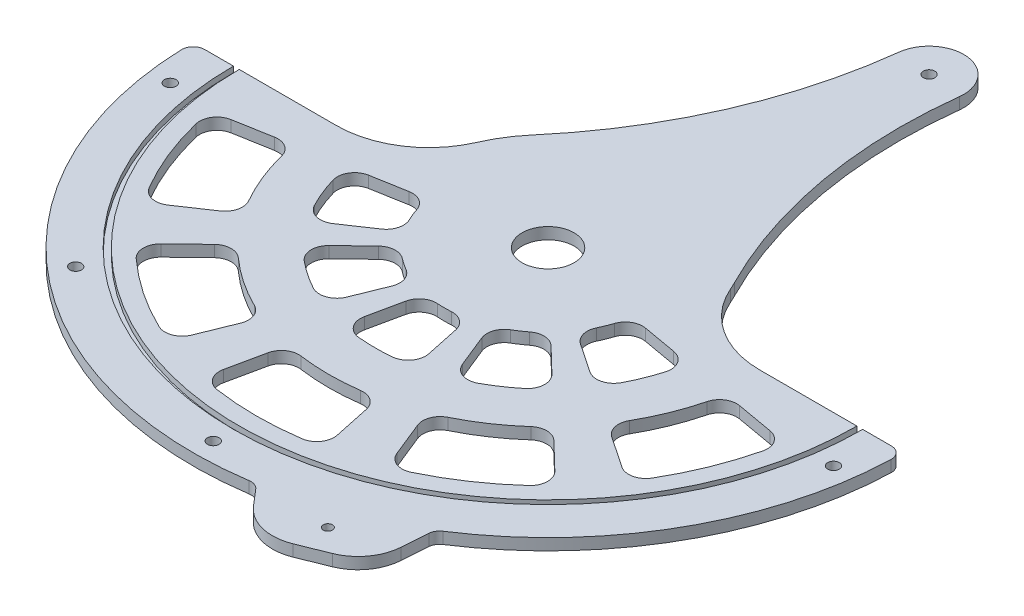
SolidWorks part; units mm, degrees
material "Polycarbonate"
ref_plane "Front Plane" through (0, 0, 0) normal (0, 0, 1) x (1, 0, 0)
ref_plane "Top Plane" through (0, 0, 0) normal (0, 1, 0) x (1, 0, 0)
ref_plane "Right Plane" through (0, 0, 0) normal (1, 0, 0) x (0, 0, -1)
sketch "Sketch1" plane through (0, 0, 0) normal (0, 1, 0) x (1, 0, 0)
  line L0 (76.2, 0) -> (173.0375, 0)
  line L3 (-173.0375, 0) -> (-76.2, 0)
  arc A0 (-169.8625, 0) -> (169.8625, 0) centre (0, 0) ccw construction
  arc A1 (173.0375, 0) -> (-173.0375, 0) centre (0, 0) cw
  arc A2 (-76.2, 0) -> (76.2, 0) centre (0, 0) cw
  dimension "D1" = 169.8625
  dimension "D2" = 3.175
  dimension "D4" = 76.2
extrude "Boss-Extrude1" add sketch "Sketch1" along normal mid plane 6.35
sketch "Sketch2" plane through (0, 3.175, 0) normal (0, 1, 0) x (1, 0, 0)
  line L0 (-76.2, 0) -> (-173.0375, 0) construction
  line L2 (173.0375, 0) -> (76.2, 0) construction
  line L3 (-78.9658, -53.2631) -> (-47.3795, -31.9579)
  line L4 (-56.2818, -9.924) -> (-93.8029, -16.54)
  line L5 (-60.0635, -148.6623) -> (-45.1963, -111.8647)
  line L6 (-157.9016, -27.8423) -> (-132.9258, -89.6596) construction
  line L7 (-86.7883, -83.8105) -> (-115.3371, -111.3798)
  line L8 (-35.6813, -88.3143) -> (-21.4088, -52.9886)
  line L9 (-41.1103, -39.6997) -> (-68.5171, -66.1662)
  line L10 (-132.9258, -89.6596) -> (-100.0234, -67.4666)
  line L11 (-118.8171, -20.9507) -> (-157.9016, -27.8423)
  line L12 (33.336, -156.8337) -> (25.0845, -118.0135)
  line L13 (-118.8171, -20.9507) -> (-100.0234, -67.4666) construction
  line L14 (-25.0845, -118.0135) -> (-33.336, -156.8337)
  line L15 (19.8036, -93.1686) -> (11.8822, -55.9011)
  line L16 (-11.8822, -55.9011) -> (-19.8036, -93.1686)
  line L17 (115.3371, -111.3798) -> (86.7883, -83.8105)
  line L18 (45.1963, -111.8647) -> (60.0635, -148.6623)
  line L19 (68.5171, -66.1662) -> (41.1103, -39.6997)
  line L20 (21.4088, -52.9886) -> (35.6813, -88.3143)
  line L21 (157.9016, -27.8423) -> (118.8171, -20.9507)
  line L22 (100.0234, -67.4666) -> (132.9258, -89.6596)
  line L23 (93.8029, -16.54) -> (56.2818, -9.924)
  line L24 (47.3795, -31.9579) -> (78.9658, -53.2631)
  line L25 (157.9016, -14.9611) -> (157.9016, -27.8423) construction
  line L26 (157.9016, -27.8423) -> (170.7829, -27.8423) construction
  line L27 (-30.1025, -103.6679) -> (0, 0) construction
  line L28 (-111.8647, -45.1963) -> (-88.3143, -35.6813) construction
  arc A0 (-157.9016, -27.8423) -> (-132.9258, -89.6596) centre (0, 0) ccw
  arc A1 (-93.8029, -16.54) -> (-78.9658, -53.2631) centre (0, 0) ccw
  arc A2 (-56.2818, -9.924) -> (-47.3795, -31.9579) centre (0, 0) ccw
  arc A3 (-86.7883, -83.8105) -> (-45.1963, -111.8647) centre (0, 0) ccw
  arc A4 (-173.0375, 0) -> (173.0375, 0) centre (0, 0) ccw construction
  arc A5 (-118.8171, -20.9507) -> (-100.0234, -67.4666) centre (0, 0) ccw
  arc A6 (-115.3371, -111.3798) -> (-60.0635, -148.6623) centre (0, 0) ccw
  arc A7 (-68.5171, -66.1662) -> (-35.6813, -88.3143) centre (0, 0) ccw
  arc A8 (-41.1103, -39.6997) -> (-21.4088, -52.9886) centre (0, 0) ccw
  arc A9 (-25.0845, -118.0135) -> (25.0845, -118.0135) centre (0, 0) ccw
  arc A10 (-33.336, -156.8337) -> (33.336, -156.8337) centre (0, 0) ccw
  arc A11 (-19.8036, -93.1686) -> (19.8036, -93.1686) centre (0, 0) ccw
  arc A12 (-11.8822, -55.9011) -> (11.8822, -55.9011) centre (0, 0) ccw
  arc A13 (45.1963, -111.8647) -> (86.7883, -83.8105) centre (0, 0) ccw
  arc A14 (60.0635, -148.6623) -> (115.3371, -111.3798) centre (0, 0) ccw
  arc A15 (35.6813, -88.3143) -> (68.5171, -66.1662) centre (0, 0) ccw
  arc A16 (21.4088, -52.9886) -> (41.1103, -39.6997) centre (0, 0) ccw
  arc A17 (100.0234, -67.4666) -> (118.8171, -20.9507) centre (0, 0) ccw
  arc A18 (132.9258, -89.6596) -> (157.9016, -27.8423) centre (0, 0) ccw
  arc A19 (78.9658, -53.2631) -> (93.8029, -16.54) centre (0, 0) ccw
  arc A20 (47.3795, -31.9579) -> (56.2818, -9.924) centre (0, 0) ccw
  arc A21 (-173.0375, 0) -> (173.0375, 0) centre (0, 0) ccw construction
  circle A22 centre (0, 0) radius 50.8 construction
  circle A23 centre (-30.1025, -103.6679) radius 61.9125 construction
  circle A24 centre (-13.5019, -46.4981) radius 2.3813 construction
  circle A25 centre (0, 0) radius 107.95 construction
  point P51 (0, 0)
  point P54 (0, 0)
  point P66 (-100.0895, -40.4388)
  dimension "D1" = 12.7
  dimension "D2" = 10
  dimension "D3" = 10
  dimension "D5" = 25.4
  dimension "D6" = 57.15
  dimension "D4" = 101.6
  dimension "D8" = 123.825
  dimension "D9" = 4.7625
  dimension "D10" = 10
  dimension "D7" = 5
extrude "Cut-Extrude1" cut sketch "Sketch2" against normal through all
sketch "Sketch4" plane through (0, 0, 0) normal (0, 1, 0) x (1, 0, 0)
  line L0 (173.0375, 0) -> (195.2625, 0)
  line L4 (-195.2625, 0) -> (-173.0375, 0)
  arc A0 (-195.2625, 0) -> (195.2625, 0) centre (0, 0) ccw
  arc A1 (-173.0375, 0) -> (173.0375, 0) centre (0, 0) ccw construction
  arc A2 (-173.0375, 0) -> (173.0375, 0) centre (0, 0) ccw
  dimension "D1" = 22.225
sketch "Sketch5" plane through (0, 3.175, 0) normal (0, 1, 0) x (1, 0, 0)
  line L0 (-76.2, 0) -> (-173.0375, 0) construction
  line L1 (169.8625, 0) -> (173.0375, 0)
  line L6 (-169.8625, 0) -> (-173.0375, 0)
  arc A0 (-169.8625, 0) -> (169.8625, 0) centre (0, 0) ccw
  arc A1 (-173.0375, 0) -> (173.0375, 0) centre (0, 0) ccw construction
  arc A2 (-173.0375, 0) -> (173.0375, 0) centre (0, 0) ccw
  dimension "D1" = 3.175
extrude "Cut-Extrude2" cut sketch "Sketch5" against normal blind 3.175
extrude "Boss-Extrude2" add sketch "Sketch4" against normal mid plane 6.35 contours A0 L0 A2 L4
sketch "Sketch6" plane through (0, 3.175, 0) normal (0, 1, 0) x (1, 0, 0)
  circle A0 centre (0, 0) radius 14.2875
  dimension "D1" = 28.575
extrude "Cut-Extrude3" cut sketch "Sketch6" against normal through all
sketch "Sketch7" plane through (0, 3.175, 0) normal (0, 1, 0) x (1, 0, 0)
  line L0 (32.2069, -192.5881) -> (53.9687, -217.9881)
  line L1 (53.9687, -217.9881) -> (101.0697, -198.958)
  line L2 (101.0697, -198.958) -> (103.4662, -165.5965)
  line L4 (32.2069, -192.5881) -> (103.4662, -165.5965)
  arc A0 (-195.2625, 0) -> (195.2625, 0) centre (0, 0) ccw construction
  arc A2 (-195.2625, 0) -> (195.2625, 0) centre (0, 0) ccw construction
extrude "Boss-Extrude3" add sketch "Sketch7" against normal through all contours L4 L2 L1 L0
sketch "Sketch8" plane through (0, 3.175, 0) normal (0, 1, 0) x (-1, 0, 0)
  line L1 (-67.8365, 179.0923) -> (-77.5192, 208.4731) construction
  line L2 (-53.9687, 217.9881) -> (-101.0697, 198.958) construction
  line L3 (-32.2069, 192.5881) -> (-67.8365, 179.0923) construction
  line L4 (-67.8365, 179.0923) -> (-103.4662, 165.5965) construction
  circle A0 centre (-72.6779, 193.7827) radius 2.54
  point P8 (-72.6779, 193.7827)
  point P14 (-77.5192, 208.4731)
  dimension "D1" = 5.08
extrude "Cut-Extrude4" cut sketch "Sketch8" against normal through all
sketch "Sketch9" plane through (0, 3.175, 0) normal (0, 1, 0) x (1, 0, 0)
  line L0 (-184.15, 0) -> (-173.0375, 0) construction
  line L1 (-195.2625, 0) -> (-173.0375, 0) construction
  line L2 (-184.15, 0) -> (-195.2625, 0) construction
  line L3 (182.3899, -25.4) -> (184.15, 0) construction
  line L4 (-184.15, 0) -> (-182.3899, -25.4) construction
  line L5 (182.3899, -25.4) -> (120.9004, -138.904) construction
  line L6 (120.9004, -138.904) -> (0, -184.15) construction
  line L7 (0, -184.15) -> (-120.9004, -138.904) construction
  line L8 (-120.9004, -138.904) -> (-182.3899, -25.4) construction
  circle A0 centre (-182.3899, -25.4) radius 3.175
  circle A1 centre (-120.9004, -138.904) radius 3.175
  circle A2 centre (0, -184.15) radius 3.175
  circle A3 centre (120.9004, -138.904) radius 3.175 construction
  circle A4 centre (182.3899, -25.4) radius 3.175
  circle A5 centre (0, 0) radius 184.15 construction
  arc A6 (-173.0375, 0) -> (173.0375, 0) centre (0, 0) ccw construction
  dimension "D1" = 6.35
  dimension "D2" = 25.4
extrude "Cut-Extrude5" cut sketch "Sketch9" against normal through all
fillet "Fillet1" radius 25.4 2 edges at (53.9687, 0, 217.9881) (101.0697, 0, 198.958)
fillet "Fillet2" radius 9.525 40 edges at (45.1963, 0, 111.8647) (60.0635, 0, 148.6623) (115.3371, 0, 111.3798) (86.7883, 0, 83.8105) (35.6813, 0, 88.3143) (68.5171, 0, 66.1662) (41.1103, 0, 39.6997) (21.4088, 0, 52.9886) (56.2818, 0, 9.924) (47.3795, 0, 31.9579) (93.8029, 0, 16.54) (78.9658, 0, 53.2631) (157.9016, 0, 27.8423) (132.9258, 0, 89.6596) (118.8171, 0, 20.9507) (100.0234, 0, 67.4666) (-11.8822, 0, 55.9011) (11.8822, 0, 55.9011) (19.8036, 0, 93.1686) (33.336, 0, 156.8337) (25.0845, 0, 118.0135) (-25.0845, 0, 118.0135) (-33.336, 0, 156.8337) (-60.0635, 0, 148.6623) (-45.1963, 0, 111.8647) (-86.7883, 0, 83.8105) (-115.3371, 0, 111.3798) (-132.9258, 0, 89.6596) (-157.9016, 0, 27.8423) (-118.8171, 0, 20.9507) (-100.0234, 0, 67.4666) (-41.1103, 0, 39.6997) (-19.8036, 0, 93.1686) (-35.6813, 0, 88.3143) (-21.4088, 0, 52.9886) (-68.5171, 0, 66.1662) (-93.8029, 0, 16.54) (-56.2818, 0, 9.924) (-47.3795, 0, 31.9579) (-78.9658, 0, 53.2631)
fillet "Fillet4" radius 6.35 4 edges at (195.2625, 0, 0) (-195.2625, 0, 0) (103.4662, 0, 165.5965) (32.2069, 0, 192.5881)
fillet "Fillet3" radius 50.8 2 edges at (76.2, 0, 0) (-76.2, 0, 0)
sketch "Sketch10" plane through (0, 3.175, 0) normal (0, 1, 0) x (1, 0, 0)
  line L0 (41.1423, 185.0806) -> (3.3077, 189.5694) construction
  arc A0 (41.1423, 185.0806) -> (67.9289, 34.5268) centre (303.0074, 154.0119) ccw
  arc A2 (3.3077, 189.5694) -> (-57.964, 49.4633) centre (-258.5568, 220.638) cw
  arc A3 (3.3077, 189.5694) -> (41.1423, 185.0806) centre (22.225, 187.325) cw
  arc A4 (69.8385, 30.48) -> (-69.8385, 30.48) centre (0, 0) ccw construction
  circle A5 centre (22.225, 187.325) radius 3.175
  arc A6 (67.9289, 34.5268) -> (-57.964, 49.4633) centre (0, 0) ccw
  circle A7 centre (22.225, 187.325) radius 3.175 construction
  arc A8 (41.1423, 185.0806) -> (67.9289, 34.5268) centre (303.0074, 154.0119) ccw construction
  point P19 (22.225, 187.325)
  dimension "D1" = 19.05
  dimension "D2" = 6.35
extrude "Boss-Extrude4" add sketch "Sketch10" against normal through all contours A2 A6 A0 A3 | A5
sketch "Sketch11" plane through (0, 3.175, 0) normal (0, 1, 0) x (1, 0, 0)
  line L0 (195.1522, -6.5634) -> (195.3729, 0)
  line L1 (195.3729, 0) -> (179.3875, 0)
  line L2 (173.0375, 0) -> (188.8057, 0) construction
  line L3 (-188.8057, 0) -> (-173.0375, 0) construction
  line L4 (-179.3875, 0) -> (-195.3729, 0)
  line L5 (-195.3729, 0) -> (-195.1522, -6.5634)
  line L6 (103.2372, -168.7839) -> (104.6985, -148.4419)
  line L7 (102.2045, -183.1606) -> (103.2372, -168.7839) construction
  line L8 (34.5153, -195.2825) -> (22.1072, -180.8)
  line L9 (34.5153, -195.2825) -> (42.0912, -204.1249) construction
  arc A4 (34.5153, -195.2825) -> (28.7579, -193.1332) centre (29.6932, -199.4139) ccw
  arc A5 (106.1199, -163.9086) -> (103.2372, -168.7839) centre (109.5709, -169.2389) ccw
  arc A6 (106.1199, -163.9086) -> (195.1522, -6.5634) centre (0, 0) ccw
  arc A7 (-195.1522, -6.5634) -> (28.7579, -193.1332) centre (0, 0) ccw
  arc A8 (179.3875, 0) -> (107.2362, -143.8064) centre (0, 0) cw
  arc A9 (16.6941, -178.609) -> (-179.3875, 0) centre (0, 0) cw
  arc A10 (104.6985, -148.4419) -> (107.2362, -143.8064) centre (111.0322, -148.8969) cw
  arc A11 (22.1072, -180.8) -> (16.6941, -178.609) centre (17.2851, -184.9315) ccw
  arc A12 (106.1199, -163.9086) -> (195.1522, -6.5634) centre (0, 0) ccw construction
  arc A13 (-195.1522, -6.5634) -> (28.7579, -193.1332) centre (0, 0) ccw construction
  arc A14 (106.1199, -163.9086) -> (103.2372, -168.7839) centre (109.5709, -169.2389) ccw construction
  arc A15 (34.5153, -195.2825) -> (28.7579, -193.1332) centre (29.6932, -199.4139) ccw construction
  point P27 (19.9442, -178.2754)
  dimension "D1" = 15.875
  dimension "D2" = 6.35
extrude "Cut-Extrude6" [suppressed] cut sketch "Sketch11" against normal through all
